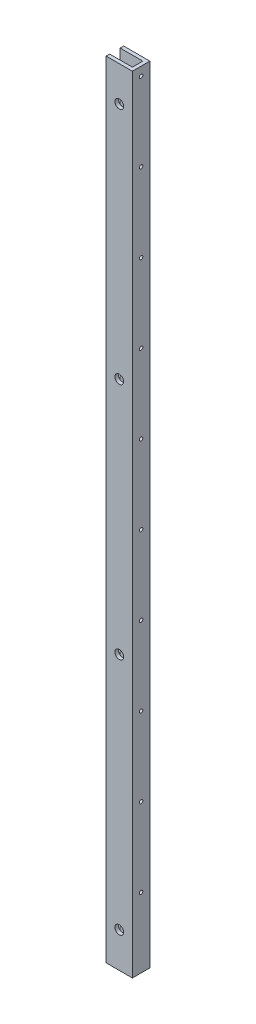
SolidWorks part; units mm, degrees
material "PP Copolymer"
ref_plane "Front Plane" through (0, 0, 0) normal (0, 0, 1) x (1, 0, 0)
ref_plane "Top Plane" through (0, 0, 0) normal (0, 1, 0) x (1, 0, 0)
ref_plane "Right Plane" through (0, 0, 0) normal (1, 0, 0) x (0, 0, -1)
sketch "Sketch1" plane through (0, 0, 0) normal (0, 1, 0) x (1, 0, 0)
  line L0 (-19.05, 3.81) -> (-19.05, 6.35)
  line L1 (0, -6.35) -> (-19.05, -6.35)
  line L2 (0, -6.35) -> (0, 6.35)
  line L3 (0, 6.35) -> (-19.05, 6.35)
  line L7 (-2.54, -3.81) -> (-19.05, -3.81)
  line L8 (-2.54, -3.81) -> (-2.54, 3.81)
  line L9 (-2.54, 3.81) -> (-19.05, 3.81)
  line L13 (-19.05, -3.81) -> (-19.05, -6.35)
  point P0 (0, 0)
  point P1 (-2.54, 0)
  point P4 (0, 0)
  point P6 (0, 0)
  dimension "D1" = 2.54
  dimension "D2" = 2.54
  dimension "D3" = 12.7
  dimension "D4" = 19.05
extrude "Boss-Extrude1" add sketch "Sketch1" along normal mid plane 571.5
sketch "Sketch2" plane through (0, 0, 0) normal (1, 0, 0) x (0, 0, -1)
  line L0 (-6.35, 285.75) -> (6.35, 285.75) construction
  circle A0 centre (0, 279.4) radius 1.27
  circle A1 centre (0, 222.25) radius 1.27
  circle A2 centre (0, 165.1) radius 1.27
  circle A3 centre (0, 107.95) radius 1.27
  circle A4 centre (0, 50.8) radius 1.27
  circle A5 centre (0, -6.35) radius 1.27
  circle A6 centre (0, -63.5) radius 1.27
  circle A7 centre (0, -120.65) radius 1.27
  circle A8 centre (0, -177.8) radius 1.27
  circle A9 centre (0, -234.95) radius 1.27
  dimension "D1" = 2.54
  dimension "D2" = 6.35
  dimension "D3" = 10
extrude "Cut-Extrude1" cut sketch "Sketch2" against normal through all
sketch "Sketch4" plane through (0, 0, 3.81) normal (0, 0, -1) x (-1, 0, 0)
  line L0 (0, 285.75) -> (19.05, 285.75) construction
  circle A0 centre (9.525, 260.35) radius 3.175
  circle A1 centre (9.525, 86.868) radius 3.175
  circle A2 centre (9.525, -86.614) radius 3.175
  circle A3 centre (9.525, -260.096) radius 3.175
  point P5 (9.525, 285.75)
  dimension "D1" = 6.35
  dimension "D2" = 25.4
  dimension "D3" = 4
extrude "Cut-Extrude2" cut sketch "Sketch4" against normal blind 140.208
sketch "Sketch5" plane through (0, 0, -6.35) normal (0, 0, -1) x (-1, 0, 0)
  line L0 (0, 285.75) -> (19.05, 285.75) construction
  circle A0 centre (9.525, 260.35) radius 6.35
  circle A1 centre (9.525, 86.7918) radius 6.35
  circle A2 centre (9.525, -86.7664) radius 6.35
  circle A3 centre (9.525, -260.3246) radius 6.35
  point P5 (9.525, 285.75)
  dimension "D1" = 12.7
  dimension "D2" = 25.4
  dimension "D3" = 4
extrude "Cut-Extrude3" cut sketch "Sketch5" against normal up to vertex (2.54 mm away)
